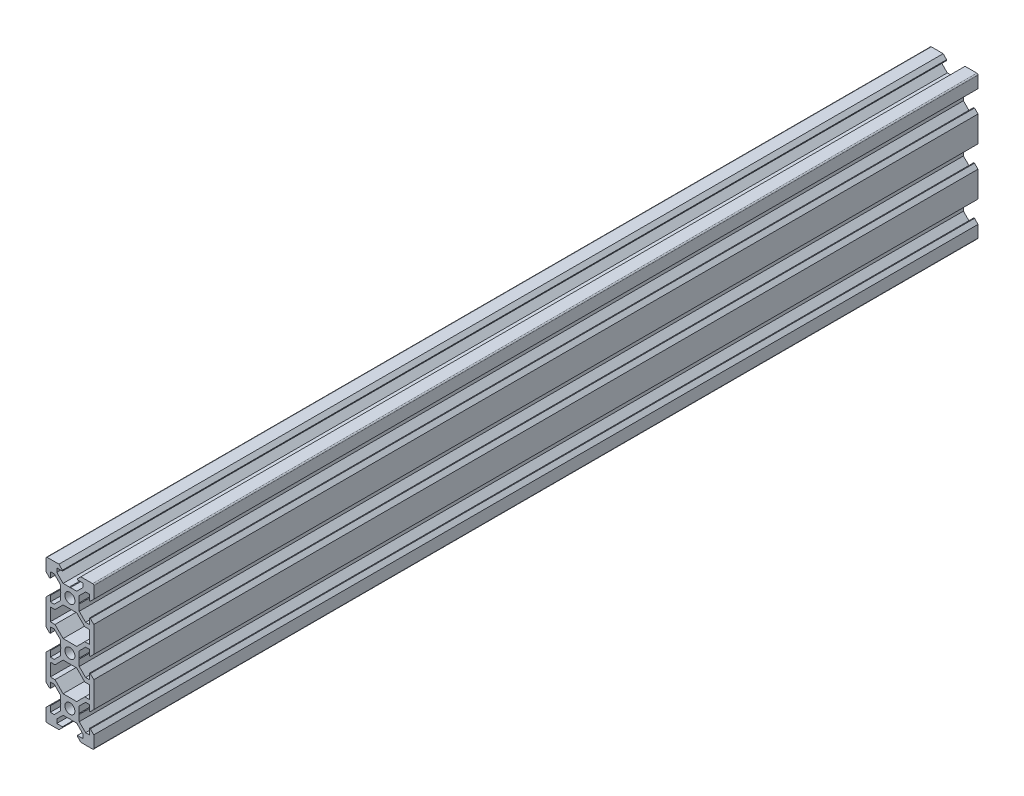
SolidWorks part; units mm, degrees
material "6061-T6 (SS)"
ref_plane "Front Plane" through (0, 0, 0) normal (0, 0, 1) x (1, 0, 0)
ref_plane "Top Plane" through (0, 0, 0) normal (0, 1, 0) x (1, 0, 0)
ref_plane "Right Plane" through (0, 0, 0) normal (1, 0, 0) x (0, 0, -1)
sketch "Sketch1" plane through (0, 0, 0) normal (0, 0, 1) x (1, 0, 0)
  line L0 (0, 0) -> (10, 0) construction
  line L1 (9.5, -30) -> (-9.5, -30)
  line L2 (10, -29.5) -> (10, 29.5)
  line L3 (9.5, 30) -> (-9.5, 30)
  line L4 (-10, -29.5) -> (-10, 29.5)
  line L5 (10, -30) -> (-10, 30) construction
  line L6 (10, 30) -> (-10, -30) construction
  circle A0 centre (0, 20) radius 2.1
  circle A1 centre (0, 0) radius 2.1
  circle A2 centre (0, -20) radius 2.1
  arc A3 (-9.5, -30) -> (-10, -29.5) centre (-9.5, -29.5) cw
  arc A4 (9.5, -30) -> (10, -29.5) centre (9.5, -29.5) ccw
  arc A5 (10, 29.5) -> (9.5, 30) centre (9.5, 29.5) ccw
  arc A6 (-9.5, 30) -> (-10, 29.5) centre (-9.5, 29.5) ccw
  point P0 (0, 0)
  line B0 (0, 20) -> (0, 30) construction
  line B1 (0, 23.69) -> (-0.21, 23.9)
  line B2 (-0.21, 23.9) -> (-2.8393, 23.9)
  line B3 (-2.8393, 23.9) -> (-5.5, 26.5607)
  line B4 (-5.5, 26.5607) -> (-5.5, 28.2)
  line B5 (-5.5, 28.2) -> (-3.125, 28.2)
  line B6 (-3.125, 28.2) -> (-3.125, 28.545)
  line B7 (-3.125, 28.545) -> (-4.58, 30)
  line B8 (-4.58, 30) -> (4.58, 30)
  line B9 (0, 20) -> (-5.9132, 25.9132) construction
  line B10 (3.125, 28.545) -> (4.58, 30)
  line B11 (3.125, 28.2) -> (3.125, 28.545)
  line B12 (5.5, 28.2) -> (3.125, 28.2)
  line B13 (5.5, 26.5607) -> (5.5, 28.2)
  line B14 (2.8393, 23.9) -> (5.5, 26.5607)
  line B15 (0.21, 23.9) -> (2.8393, 23.9)
  line B16 (0, 23.69) -> (0.21, 23.9)
  line B17 (0, 20) -> (-10, 20) construction
  line B18 (-3.69, 20) -> (-3.9, 19.79)
  line B19 (-3.9, 19.79) -> (-3.9, 17.1607)
  line B20 (-3.9, 17.1607) -> (-6.5607, 14.5)
  line B21 (-6.5607, 14.5) -> (-8.2, 14.5)
  line B22 (-8.2, 14.5) -> (-8.2, 16.875)
  line B23 (-8.2, 16.875) -> (-8.545, 16.875)
  line B24 (-8.545, 16.875) -> (-10, 15.42)
  line B25 (-10, 15.42) -> (-10, 24.58)
  line B26 (0, 20) -> (-5.9132, 14.0868) construction
  line B27 (-8.545, 23.125) -> (-10, 24.58)
  line B28 (-8.2, 23.125) -> (-8.545, 23.125)
  line B29 (-8.2, 25.5) -> (-8.2, 23.125)
  line B30 (-6.5607, 25.5) -> (-8.2, 25.5)
  line B31 (-3.9, 22.8393) -> (-6.5607, 25.5)
  line B32 (-3.9, 20.21) -> (-3.9, 22.8393)
  line B33 (-3.69, 20) -> (-3.9, 20.21)
  line B34 (0, 0) -> (-10, 0) construction
  line B35 (-3.69, 0) -> (-3.9, -0.21)
  line B36 (-3.9, -0.21) -> (-3.9, -2.8393)
  line B37 (-3.9, -2.8393) -> (-6.5607, -5.5)
  line B38 (-6.5607, -5.5) -> (-8.2, -5.5)
  line B39 (-8.2, -5.5) -> (-8.2, -3.125)
  line B40 (-8.2, -3.125) -> (-8.545, -3.125)
  line B41 (-8.545, -3.125) -> (-10, -4.58)
  line B42 (-10, -4.58) -> (-10, 4.58)
  line B43 (0, 0) -> (-5.9132, -5.9132) construction
  line B44 (-8.545, 3.125) -> (-10, 4.58)
  line B45 (-8.2, 3.125) -> (-8.545, 3.125)
  line B46 (-8.2, 5.5) -> (-8.2, 3.125)
  line B47 (-6.5607, 5.5) -> (-8.2, 5.5)
  line B48 (-3.9, 2.8393) -> (-6.5607, 5.5)
  line B49 (-3.9, 0.21) -> (-3.9, 2.8393)
  line B50 (-3.69, 0) -> (-3.9, 0.21)
  line B51 (0, -20) -> (-10, -20) construction
  line B52 (-3.69, -20) -> (-3.9, -20.21)
  line B53 (-3.9, -20.21) -> (-3.9, -22.8393)
  line B54 (-3.9, -22.8393) -> (-6.5607, -25.5)
  line B55 (-6.5607, -25.5) -> (-8.2, -25.5)
  line B56 (-8.2, -25.5) -> (-8.2, -23.125)
  line B57 (-8.2, -23.125) -> (-8.545, -23.125)
  line B58 (-8.545, -23.125) -> (-10, -24.58)
  line B59 (-10, -24.58) -> (-10, -15.42)
  line B60 (0, -20) -> (-5.9132, -25.9132) construction
  line B61 (-8.545, -16.875) -> (-10, -15.42)
  line B62 (-8.2, -16.875) -> (-8.545, -16.875)
  line B63 (-8.2, -14.5) -> (-8.2, -16.875)
  line B64 (-6.5607, -14.5) -> (-8.2, -14.5)
  line B65 (-3.9, -17.1607) -> (-6.5607, -14.5)
  line B66 (-3.9, -19.79) -> (-3.9, -17.1607)
  line B67 (-3.69, -20) -> (-3.9, -19.79)
  line B68 (0, -20) -> (0, -30) construction
  line B69 (0, -23.69) -> (0.21, -23.9)
  line B70 (0.21, -23.9) -> (2.8393, -23.9)
  line B71 (2.8393, -23.9) -> (5.5, -26.5607)
  line B72 (5.5, -26.5607) -> (5.5, -28.2)
  line B73 (5.5, -28.2) -> (3.125, -28.2)
  line B74 (3.125, -28.2) -> (3.125, -28.545)
  line B75 (3.125, -28.545) -> (4.58, -30)
  line B76 (4.58, -30) -> (-4.58, -30)
  line B77 (0, -20) -> (5.9132, -25.9132) construction
  line B78 (-3.125, -28.545) -> (-4.58, -30)
  line B79 (-3.125, -28.2) -> (-3.125, -28.545)
  line B80 (-5.5, -28.2) -> (-3.125, -28.2)
  line B81 (-5.5, -26.5607) -> (-5.5, -28.2)
  line B82 (-2.8393, -23.9) -> (-5.5, -26.5607)
  line B83 (-0.21, -23.9) -> (-2.8393, -23.9)
  line B84 (0, -23.69) -> (-0.21, -23.9)
  line B85 (0, -20) -> (10, -20) construction
  line B86 (3.69, -20) -> (3.9, -19.79)
  line B87 (3.9, -19.79) -> (3.9, -17.1607)
  line B88 (3.9, -17.1607) -> (6.5607, -14.5)
  line B89 (6.5607, -14.5) -> (8.2, -14.5)
  line B90 (8.2, -14.5) -> (8.2, -16.875)
  line B91 (8.2, -16.875) -> (8.545, -16.875)
  line B92 (8.545, -16.875) -> (10, -15.42)
  line B93 (10, -15.42) -> (10, -24.58)
  line B94 (0, -20) -> (5.9132, -14.0868) construction
  line B95 (8.545, -23.125) -> (10, -24.58)
  line B96 (8.2, -23.125) -> (8.545, -23.125)
  line B97 (8.2, -25.5) -> (8.2, -23.125)
  line B98 (6.5607, -25.5) -> (8.2, -25.5)
  line B99 (3.9, -22.8393) -> (6.5607, -25.5)
  line B100 (3.9, -20.21) -> (3.9, -22.8393)
  line B101 (3.69, -20) -> (3.9, -20.21)
  line B102 (0, 0) -> (10, 0) construction
  line B103 (3.69, 0) -> (3.9, 0.21)
  line B104 (3.9, 0.21) -> (3.9, 2.8393)
  line B105 (3.9, 2.8393) -> (6.5607, 5.5)
  line B106 (6.5607, 5.5) -> (8.2, 5.5)
  line B107 (8.2, 5.5) -> (8.2, 3.125)
  line B108 (8.2, 3.125) -> (8.545, 3.125)
  line B109 (8.545, 3.125) -> (10, 4.58)
  line B110 (10, 4.58) -> (10, -4.58)
  line B111 (0, 0) -> (5.9132, 5.9132) construction
  line B112 (8.545, -3.125) -> (10, -4.58)
  line B113 (8.2, -3.125) -> (8.545, -3.125)
  line B114 (8.2, -5.5) -> (8.2, -3.125)
  line B115 (6.5607, -5.5) -> (8.2, -5.5)
  line B116 (3.9, -2.8393) -> (6.5607, -5.5)
  line B117 (3.9, -0.21) -> (3.9, -2.8393)
  line B118 (3.69, 0) -> (3.9, -0.21)
  line B119 (0, 20) -> (10, 20) construction
  line B120 (3.69, 20) -> (3.9, 20.21)
  line B121 (3.9, 20.21) -> (3.9, 22.8393)
  line B122 (3.9, 22.8393) -> (6.5607, 25.5)
  line B123 (6.5607, 25.5) -> (8.2, 25.5)
  line B124 (8.2, 25.5) -> (8.2, 23.125)
  line B125 (8.2, 23.125) -> (8.545, 23.125)
  line B126 (8.545, 23.125) -> (10, 24.58)
  line B127 (10, 24.58) -> (10, 15.42)
  line B128 (0, 20) -> (5.9132, 25.9132) construction
  line B129 (8.545, 16.875) -> (10, 15.42)
  line B130 (8.2, 16.875) -> (8.545, 16.875)
  line B131 (8.2, 14.5) -> (8.2, 16.875)
  line B132 (6.5607, 14.5) -> (8.2, 14.5)
  line B133 (3.9, 17.1607) -> (6.5607, 14.5)
  line B134 (3.9, 19.79) -> (3.9, 17.1607)
  line B135 (3.69, 20) -> (3.9, 19.79)
  line B136 (-8.2, 7.3) -> (-8.2, 12.7)
  line B137 (-8.2, 12.7) -> (-6.2393, 12.7)
  line B138 (-6.2393, 12.7) -> (-2.8393, 16.1)
  line B139 (-2.8393, 16.1) -> (2.8393, 16.1)
  line B140 (0, 16.1) -> (0, 10) construction
  line B141 (0, 10) -> (-8.2, 10) construction
  line B142 (6.2393, 12.7) -> (2.8393, 16.1)
  line B143 (8.2, 12.7) -> (6.2393, 12.7)
  line B144 (8.2, 7.3) -> (8.2, 12.7)
  line B145 (8.2, 7.3) -> (6.2393, 7.3)
  line B146 (6.2393, 7.3) -> (2.8393, 3.9)
  line B147 (-2.8393, 3.9) -> (2.8393, 3.9)
  line B148 (-6.2393, 7.3) -> (-2.8393, 3.9)
  line B149 (-8.2, 7.3) -> (-6.2393, 7.3)
  line B150 (0, 16.1) -> (0, 20) construction
  line B151 (0, 20) -> (-5.0927, 14.9073) construction
  line B152 (-8.2, -12.7) -> (-8.2, -7.3)
  line B153 (-8.2, -7.3) -> (-6.2393, -7.3)
  line B154 (-6.2393, -7.3) -> (-2.8393, -3.9)
  line B155 (-2.8393, -3.9) -> (2.8393, -3.9)
  line B156 (0, -3.9) -> (0, -10) construction
  line B157 (0, -10) -> (-8.2, -10) construction
  line B158 (6.2393, -7.3) -> (2.8393, -3.9)
  line B159 (8.2, -7.3) -> (6.2393, -7.3)
  line B160 (8.2, -12.7) -> (8.2, -7.3)
  line B161 (8.2, -12.7) -> (6.2393, -12.7)
  line B162 (6.2393, -12.7) -> (2.8393, -16.1)
  line B163 (-2.8393, -16.1) -> (2.8393, -16.1)
  line B164 (-6.2393, -12.7) -> (-2.8393, -16.1)
  line B165 (-8.2, -12.7) -> (-6.2393, -12.7)
  line B166 (0, -3.9) -> (0, 0) construction
  line B167 (0, 0) -> (-5.0927, -5.0927) construction
  dimension "D3" = 4.2
  dimension "D5" = 0.5
  dimension "D1" = 20
  dimension "D2" = 60
  dimension "D4" = 40
sketch_block_instance "V Slot 1-4"
sketch_block "V Slot 1" parameters "D1"=10, "D2"=11, "D3"=4.3, "D4"=1.8, "D5"=0.21, "D6"=45, "D7"=9.16, "D8"=1.5, "D9"=6.25
sketch_block_instance "V Slot 1-5"
sketch_block_instance "V Slot 1-6"
sketch_block_instance "V Slot 1-7"
sketch_block_instance "V Slot 1-8"
sketch_block_instance "V Slot 1-9"
sketch_block_instance "V Slot 1-10"
sketch_block_instance "V Slot 1-11"
sketch_block_instance "Center Cutout 1-1"
sketch_block "Center Cutout 1" parameters "D1"=5.4, "D2"=12.2, "D3"=8.2, "D4"=45, "D5"=10, "D6"=1.5
sketch_block_instance "Center Cutout 1-2"
extrude "Boss-Extrude1" add sketch "Sketch1" along normal blind 370 contours B135 B120 B121 B122 B123 B124 B125 B126 L2 A5 L3 B10 B11 B12 B13 B14 B15 B16 B1 B2 B3 B4 B5 B6 B7 A6 L4 B27 B28 B29 B30 B31 B32 B33 B18 B19 B20 B21 B22 B23 B24 B44 B45 B46 B47 B48 B49 B50 B35
